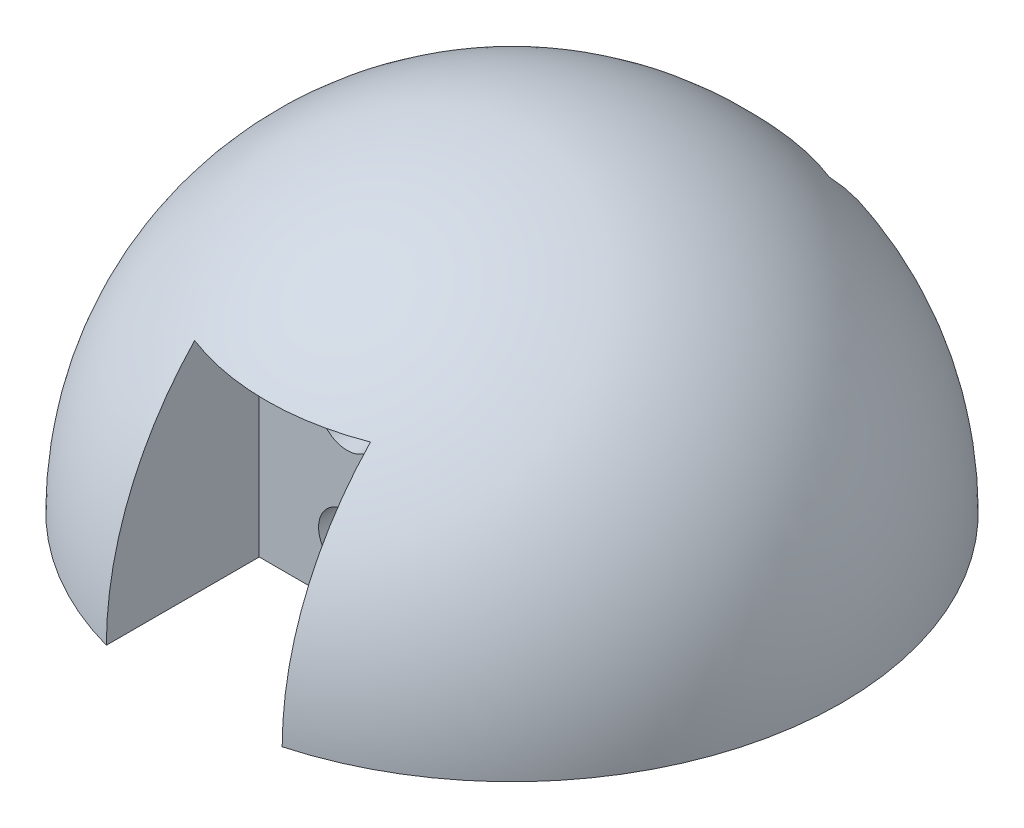
SolidWorks part; units mm, degrees
ref_plane "Front Plane" through (0, 0, 0) normal (0, 0, 1) x (1, 0, 0)
ref_plane "Top Plane" through (0, 0, 0) normal (0, 1, 0) x (1, 0, 0)
ref_plane "Right Plane" through (0, 0, 0) normal (1, 0, 0) x (0, 0, -1)
sketch "Sketch2" plane through (0, 0, 0) normal (0, 0, 1) x (1, 0, 0)
  line L0 (0, 0) -> (0, 30)
  line L1 (0, 0) -> (-30, 0)
  arc A0 (0, 30) -> (-30, 0) centre (0, 0) ccw
  dimension "D1" = 30
revolve "Revolve1" add sketch "Sketch2" angle 360 about L0
sketch "Sketch3" plane through (0, 0, 0) normal (0, -1, 0) x (1, 0, 0)
  line L1 (-10, 5) -> (10, 5)
  line L2 (-10, 5) -> (-10, -5)
  line L3 (-10, -5) -> (10, -5)
  line L4 (10, 5) -> (10, -5)
  dimension "D1" = 10
  dimension "D2" = 10
  dimension "D3" = 5
  dimension "D4" = 5
extrude "Cut-Extrude1" cut sketch "Sketch3" against normal blind 20
sketch "Sketch4" plane through (0, 0, 5) normal (0, 0, -1) x (-1, 0, 0)
  line L0 (-10, 20) -> (10, 20) construction
  line L1 (10, 20) -> (10, 0) construction
  line L2 (-10, 20) -> (-10, 0) construction
  circle A0 centre (0, 15) radius 2.6
  circle A1 centre (0, 5.0501) radius 2.6
  dimension "D1" = 5.2
  dimension "D2" = 5.2
  dimension "D3" = 9.9499
  dimension "D4" = 5
  dimension "D5" = 10
  dimension "D6" = 10
extrude "Cut-Extrude2" cut sketch "Sketch4" against normal through all
ref_plane "Plane1" through (0, 0, 30) normal (0, 0, 1) x (1, 0, 0)
sketch "Sketch6" plane through (0, 0, 30) normal (0, 0, 1) x (1, 0, 0)
  line L0 (-30, 0) -> (30, 0) construction
  line L1 (-8, 0) -> (8, 0)
  line L2 (-8, 0) -> (-8, 20)
  line L3 (-8, 20) -> (8, 20)
  line L4 (8, 0) -> (8, 20)
  dimension "D1" = 8
  dimension "D2" = 8
  dimension "D3" = 20
sketch "Sketch7" plane through (0, 0, -5) normal (0, 0, 1) x (1, 0, 0)
  line L0 (-10, 20) -> (10, 20) construction
  line L1 (10, 20) -> (10, 0) construction
  line L2 (-10, 20) -> (-10, 0) construction
  circle A0 centre (0, 5) radius 2.6
  circle A1 centre (0, 15) radius 2.6
  dimension "D1" = 5.2
  dimension "D2" = 5.2
  dimension "D3" = 5
  dimension "D4" = 10
  dimension "D5" = 10
  dimension "D6" = 10
extrude "Cut-Extrude4" cut sketch "Sketch7" against normal through all contours A1 | A0
ref_plane "Plane2" through (0, 0, -30) normal (0, 0, 1) x (1, 0, 0)
sketch "Sketch8" plane through (0, 0, -30) normal (0, 0, 1) x (1, 0, 0)
  line L0 (-30, 0) -> (30, 0) construction
  line L1 (-8, 0) -> (8, 0)
  line L2 (-8, 0) -> (-8, 20)
  line L3 (-8, 20) -> (8, 20)
  line L4 (8, 0) -> (8, 20)
  dimension "D1" = 8
  dimension "D2" = 8
  dimension "D3" = 20
extrude "Cut-Extrude9" cut sketch "Sketch8" along normal blind 15
extrude "Cut-Extrude10" cut sketch "Sketch6" against normal blind 15
